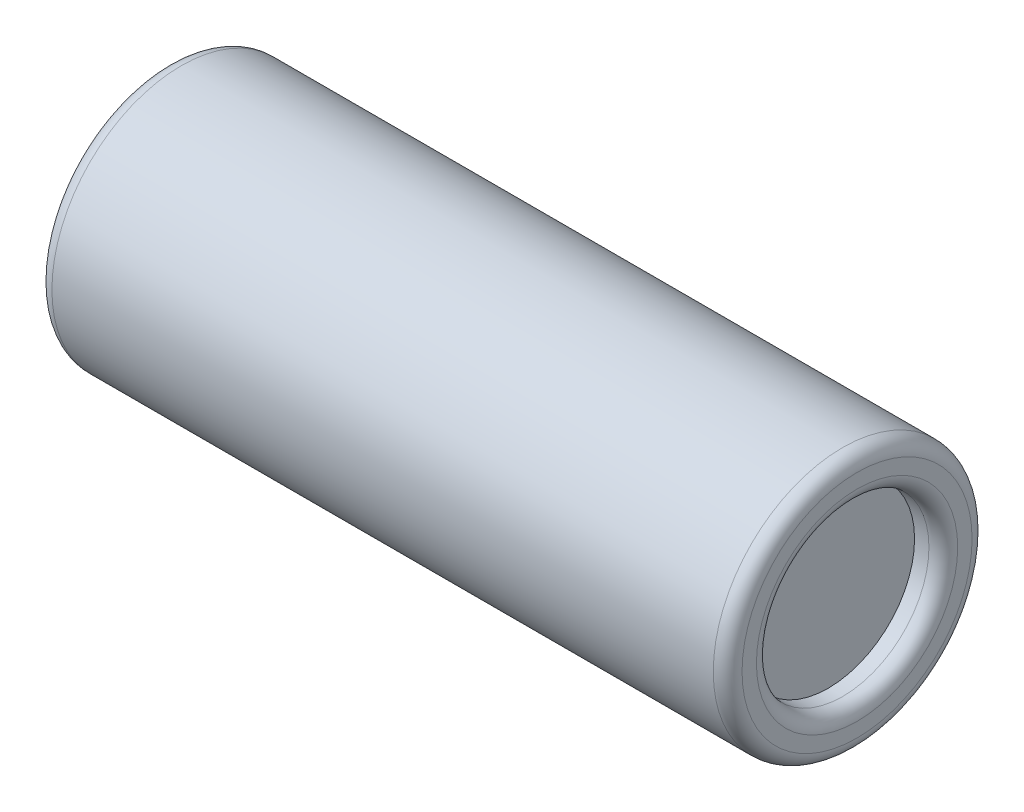
SolidWorks part; units mm, degrees
ref_plane "Front Plane" through (0, 0, 0) normal (0, 0, 1) x (1, 0, 0)
ref_plane "Top Plane" through (0, 0, 0) normal (0, 1, 0) x (1, 0, 0)
ref_plane "Right Plane" through (0, 0, 0) normal (1, 0, 0) x (0, 0, -1)
sketch "Sketch1" plane through (0, 0, 0) normal (1, 0, 0) x (0, 0, -1)
  circle A0 centre (0, 0) radius 4.5
  dimension "D1" = 9
extrude "Extrude1" add sketch "Sketch1" along normal blind 24
fillet "Fillet1" radius 0.5 1 edges at (0, 0, -4.5)
sketch "Sketch2" plane through (24, 0, 0) normal (1, 0, 0) x (0, 0, -1)
  circle A0 centre (0, 0) radius 3
  dimension "D1" = 6
extrude "Extrude2" cut sketch "Sketch2" against normal blind 1
fillet "Fillet2" radius 0.5 2 edges at (24, 0, -3) (24, 0, -4.5)
sketch "Sketch3" plane through (23, 0, 0) normal (1, 0, 0) x (0, 0, -1)
  circle A0 centre (0, 0) radius 0.5
  dimension "D1" = 1
